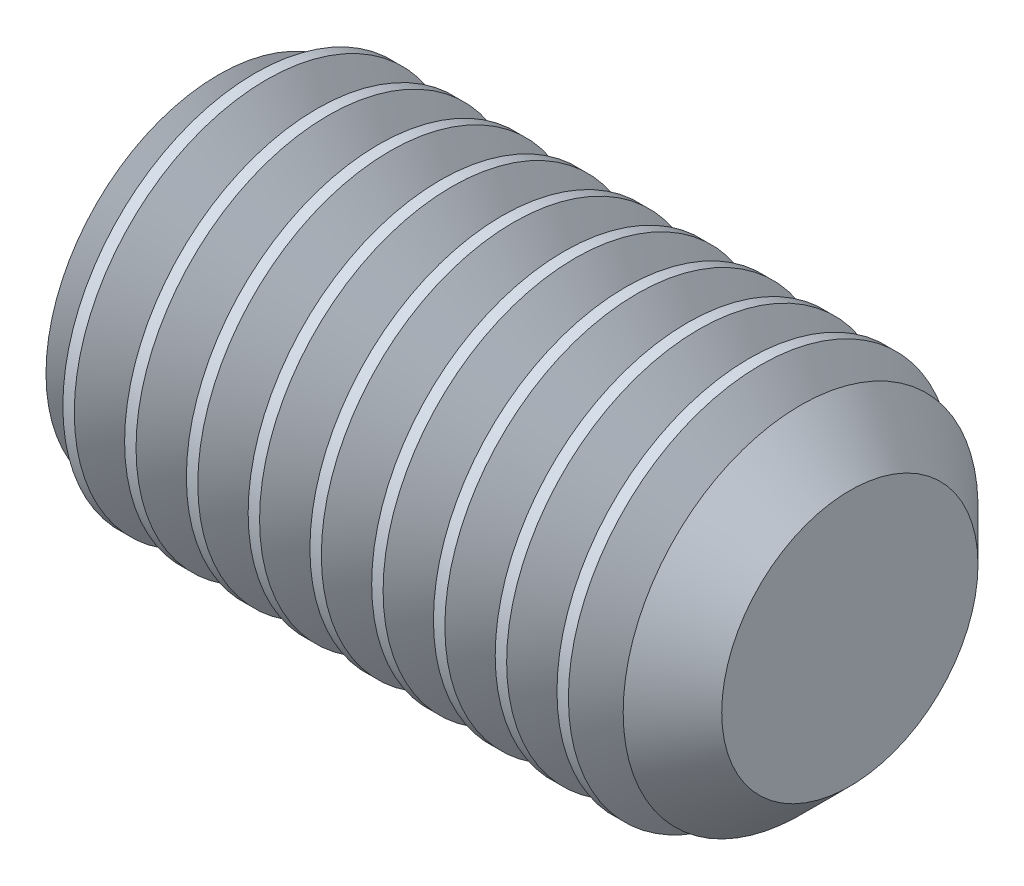
SolidWorks part; units mm, degrees
revolve "BaseBody" add sketch "BodySke" angle 360 about L5
sketch "BodySke" plane through (0, 0, 0) normal (0, 0, 1) x (1, 0, 0)
  line L0 (0, 0) -> (0, 1.2195)
  line L1 (0, 1.2195) -> (0.1619, 1.5)
  line L2 (0.1619, 1.5) -> (4.5, 1.5)
  line L3 (4.5, 1.5) -> (5, 1)
  line L4 (5, 0) -> (0, 0)
  line L5 (-12.7, 0) -> (88.9, 0) construction
  line L6 (5, 1) -> (5, 0)
  line L7 (5, 1) -> (5, 10.525) construction
  line L8 (0, -1.2195) -> (0.1619, -1.5) construction
  line L9 (0.5, 15.875) -> (0.5, -3.175) construction
  line L10 (4.5, -1.5) -> (5, -1) construction
  dimension "Diameter" = 3
  dimension "Drive_ch_ang" = 60
  dimension "Minor_dia" = 2.439
  dimension "Cup_nose_ang" = 45
  dimension "Cup_dia" = 2
  dimension "Length" = 5
  dimension "Advance" = 0.5
cosmetic thread "ThreadCosmetic" [suppressed] parameters "Thread_minor"=2.439
ref_plane "Plane1" through (0, 0, 0) normal (0, 0, 1) x (1, 0, 0)
ref_plane "Plane2" through (0, 0, 0) normal (0, 1, 0) x (1, 0, 0)
ref_plane "Plane3" through (0, 0, 0) normal (1, 0, 0) x (0, 0, -1)
other "Configuration Table"
sketch "Sketch2" plane through (0, 0, 0) normal (-1, 0, 0) x (0, 0, 1)
  line L0 (0.433, 0.75) -> (-0.433, 0.75)
  line L1 (-0.433, 0.75) -> (-0.866, 0)
  line L2 (0.433, 0.75) -> (0.866, 0)
  line L3 (0.433, -0.75) -> (0.866, 0)
  line L4 (0.433, -0.75) -> (-0.433, -0.75)
  line L5 (-0.433, -0.75) -> (-0.866, 0)
  dimension "Hex_size" = 1.5
  dimension "D2" = 0.75
  dimension "D3" = 0.75
extrude "Hex" cut sketch "Sketch2" against normal blind 2.1
sketch "Sketch4" plane through (0, 4.7709, -0.5249) normal (-1, 0, 0) x (0, 0, 1)
  line L0 (0.5249, -4.7709) -> (1.3124, -4.7709)
  line L1 (0.5249, -4.7709) -> (6.6732, -1.2211) construction
  line L2 (0.5249, -4.7709) -> (0.9186, -4.0889)
  line L3 (1.153, -4.6137) -> (1.2782, -4.5415)
  line L4 (0.975, -4.3054) -> (1.1002, -4.2332)
  arc A0 (1.153, -4.6137) -> (0.975, -4.3054) centre (0.5249, -4.7709) ccw
  arc A1 (1.3124, -4.7709) -> (1.2782, -4.5415) centre (0.5249, -4.7709) ccw
  arc A2 (0.9186, -4.0889) -> (1.1002, -4.2332) centre (0.5249, -4.7709) cw
  circle A3 centre (0.5249, -4.7709) radius 0.6475 construction
  circle A4 centre (0.5249, -4.7709) radius 0.7875 construction
  dimension "Spline_n_dim" = 1.295
  dimension "Spline_m_dim" = 1.575
  dimension "D1" = 30
  dimension "Spline_a_dim" = 60
  dimension "Spline_p_dim" = 0.356
  dimension "D3" = 0.178
extrude "Spline6" [suppressed] cut sketch "Sketch4" against normal blind 1.2
pattern_circular "CirPattern1" [suppressed] count 6 every 60 about axis through (-12.7, 0, 0) along (1, 0, 0)
sketch "Sketch5" plane through (0, 0.6556, 6.6316) normal (-1, 0, 0) x (0, 0, 1)
  line L0 (-6.6316, -0.6556) -> (-5.8441, -0.6556)
  line L1 (-6.6316, -0.6556) -> (-1.6115, 4.3645) construction
  line L2 (-6.6316, -0.6556) -> (-6.6316, 0.1319)
  line L3 (-6.0479, -0.3236) -> (-5.9633, -0.239)
  line L4 (-6.2996, -0.0719) -> (-6.215, 0.0127)
  line L5 (-6.2996, -0.0719) -> (-6.0479, -0.3236)
  arc A1 (-5.8441, -0.6556) -> (-5.9633, -0.239) centre (-6.6316, -0.6556) ccw
  arc A2 (-6.6316, 0.1319) -> (-6.215, 0.0127) centre (-6.6316, -0.6556) cw
  circle A3 centre (-6.6316, -0.6556) radius 0.6475 construction
  circle A4 centre (-6.6316, -0.6556) radius 0.7875 construction
  dimension "Spline_n_dim" = 1.295
  dimension "Spline_m_dim" = 1.575
  dimension "Spline_p_dim" = 0.356
  dimension "D3" = 0.178
  dimension "D1" = 45
  dimension "Spline_a_dim" = 90
extrude "Spline4" [suppressed] cut sketch "Sketch5" against normal blind 1.2
pattern_circular "CirPattern2" [suppressed] count 4 every 90 about axis through (-12.7, 0, 0) along (1, 0, 0)
sketch "ThdSchSke" plane through (0, 0, 0) normal (0, 0, 1) x (1, 0, 0)
  line L0 (0.1619, -1.2195) -> (-0.0345, -1.5)
  line L1 (0.1619, -1.2195) -> (0.3584, -1.5)
  line L2 (0.3584, -1.5) -> (0.3584, -1.875)
  line L3 (-3.175, 0) -> (5.1513, 0) construction
  line L4 (0.1619, 1.5) -> (0.1619, -1.5) construction
  line L5 (0.3584, -1.875) -> (-0.0345, -1.875)
  line L6 (-0.0345, -1.875) -> (-0.0345, -1.5)
  dimension "Thread_minor" = 2.439
  dimension "Diameter" = 3
revolve "ThreadSchematic" cut sketch "ThdSchSke" angle 360 about L3
pattern_linear "ThdSchPat" count 10 spacing 0.482 along (1, 0, 0) of "ThreadSchematic"
equation "\"D2@Sketch2\" = \"Hex_size@Sketch2\" / 2"
equation "\"D3@Sketch2\" = \"Hex_size@Sketch2\" / 2"
equation "\"Thread_minor@ThreadCosmetic\" = \"Minor_dia@BodySke\""
equation "\"D1@Sketch4\" = \"Spline_a_dim@Sketch4\" / 2"
equation "\"D3@Sketch4\" = \"Spline_p_dim@Sketch4\" / 2"
equation "\"D2@CirPattern1\" = \"Spline_a_dim@Sketch4\""
equation "\"Num_teeth@CirPattern1\" = 360 / \"D2@CirPattern1\""
equation "\"Spline_a_dim@Sketch5\" = 90"
equation "\"Spline_p_dim@Sketch5\" = \"Spline_p_dim@Sketch4\""
equation "\"Spline_m_dim@Sketch5\" = \"Spline_m_dim@Sketch4\""
equation "\"Spline_n_dim@Sketch5\" = \"Spline_n_dim@Sketch4\""
equation "\"D1@Sketch5\" = \"Spline_a_dim@Sketch5\" / 2"
equation "\"D3@Sketch5\" = \"Spline_p_dim@Sketch5\" / 2"
equation "\"Key_eng@Spline4\" = \"Key_eng@Spline6\""
equation "\"Thread_minor@ThdSchSke\" = \"Thread_minor@ThreadCosmetic\""
equation "\"Diameter@ThdSchSke\" = \"Diameter@BodySke\""
equation "\"Overcut@ThdSchSke\" = \"Diameter@BodySke\" * 1.25"
equation "\"Num_threads@ThdSchPat\" = int( (\"Length@BodySke\" - ( ( ( \"Diameter@BodySke\" - \"Minor_dia@BodySke\" ) * 0.5 ) / tan( \"Drive_ch_ang@BodySke\" * 0.017453292 ) ) - ( ( ( \"Diameter@BodySke\" - \"Cup_dia@BodySke\" ) * 0.5 ) * tan( \"Cup_nose_ang@BodySke\" * 0.017453292 ) ) ) / \"Advance@BodySke\" + 0.999 )  + 1"
equation "\"Advance@ThdSchPat\" = (\"Length@BodySke\" - ( ( ( \"Diameter@BodySke\" - \"Minor_dia@BodySke\" ) * 0.5 ) / tan( \"Drive_ch_ang@BodySke\" * 0.017453292 ) ) - ( ( ( \"Diameter@BodySke\" - \"Cup_dia@BodySke\" ) * 0.5 ) * tan( \"Cup_nose_ang@BodySke\" * 0.017453292 ) ) ) /  (\"Num_threads@ThdSchPat\" - 1) 'relax it"
equation "' \"Num_threads@ThdSchPat\" = \"Num_threads@ThdSchPat\" - sgn( \"Num_threads@ThdSchPat\" - 1) '---chamfered tips only---"
